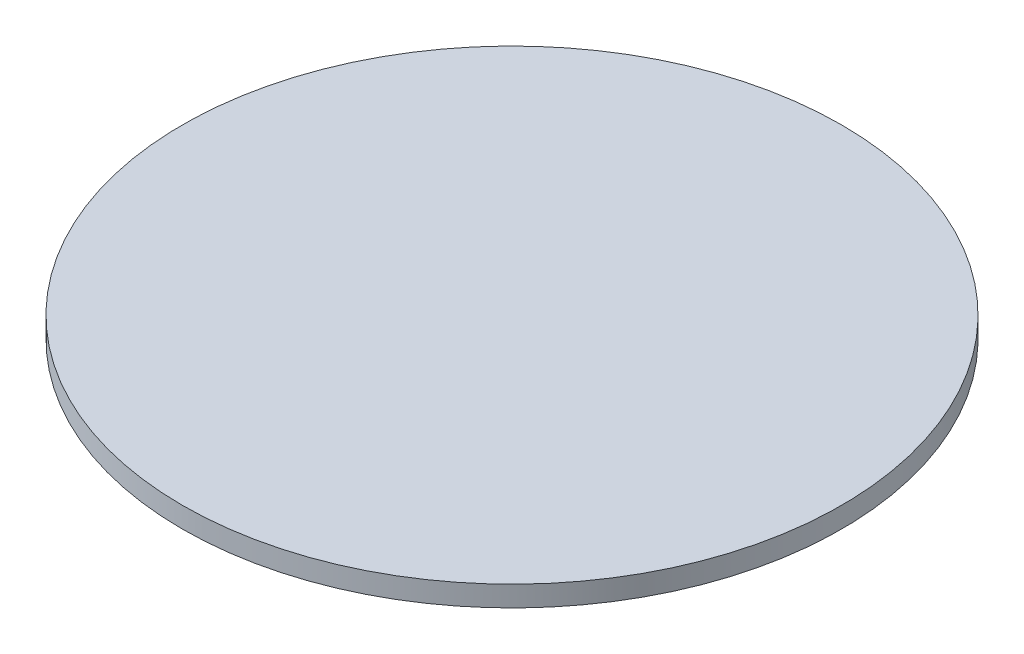
SolidWorks part; units mm, degrees
ref_plane "Front Plane" through (0, 0, 0) normal (0, 0, 1) x (1, 0, 0)
ref_plane "Top Plane" through (0, 0, 0) normal (0, 1, 0) x (1, 0, 0)
ref_plane "Right Plane" through (0, 0, 0) normal (1, 0, 0) x (0, 0, -1)
sketch "Sketch1" plane through (0, 0, 0) normal (0, 1, 0) x (1, 0, 0)
  circle A0 centre (0, 0) radius 50.8
  dimension "D1" = 101.6
extrude "Boss-Extrude1" add sketch "Sketch1" along normal blind 3.175 contours A0
